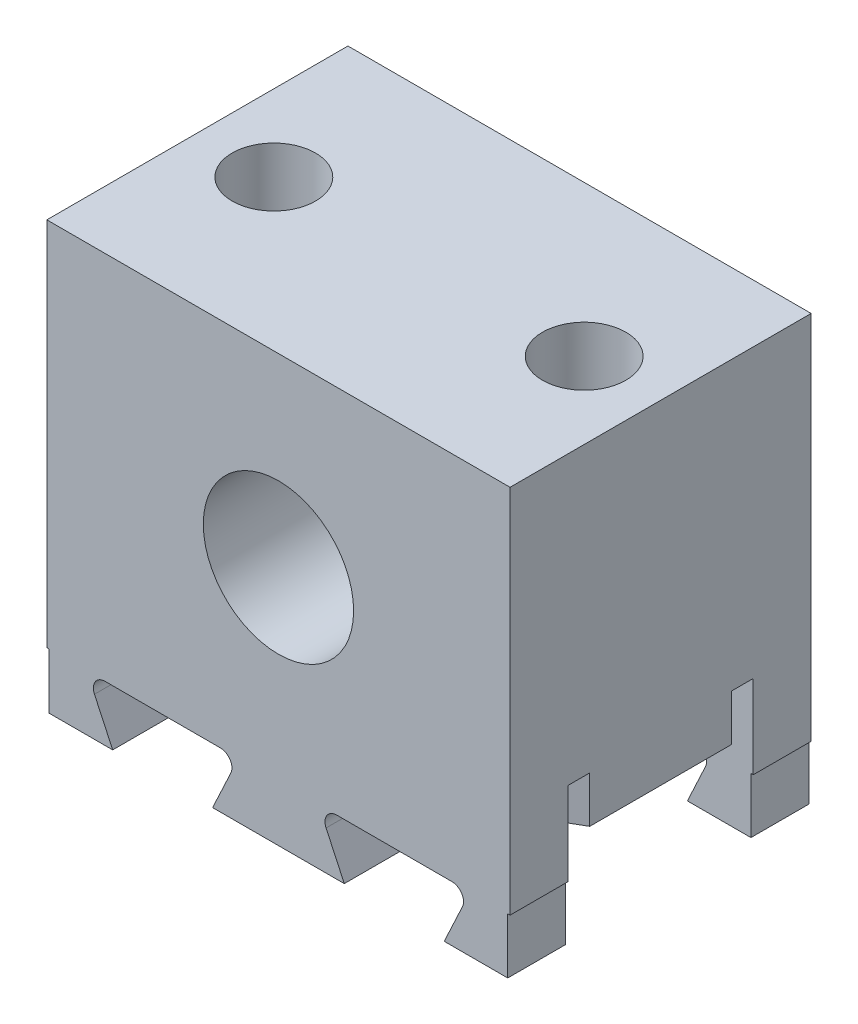
SolidWorks part; units mm, degrees
ref_plane "Front Plane" through (0, 0, 0) normal (0, 0, 1) x (1, 0, 0)
ref_plane "Top Plane" through (0, 0, 0) normal (0, 1, 0) x (1, 0, 0)
ref_plane "Right Plane" through (0, 0, 0) normal (1, 0, 0) x (0, 0, -1)
sketch "Sketch1" plane through (0, 0, 0) normal (0, 0, 1) x (1, 0, 0)
  line L1 (0, 0) -> (20, 0)
  line L2 (0, 0) -> (0, 16)
  line L3 (0, 16) -> (20, 16)
  line L4 (20, 0) -> (20, 16)
  dimension "D1" = 20
  dimension "D2" = 16
extrude "Boss-Extrude1" add sketch "Sketch1" along normal blind 13
sketch "Sketch2" plane through (0, 0, 0) normal (0, -1, 0) x (1, 0, 0)
  line L5 (0, 6.5) -> (20, 6.5) construction
  line L6 (0, 13) -> (0, 0) construction
  line L7 (20, 13) -> (20, 0) construction
  line L9 (0, 2.5) -> (20, 2.5)
  line L10 (0, 2.5) -> (0, 10.5)
  line L11 (0, 10.5) -> (20, 10.5)
  line L12 (20, 2.5) -> (20, 10.5)
  line L13 (0, 2.5) -> (20, 10.5) construction
  line L14 (0, 10.5) -> (20, 2.5) construction
  point P6 (10, 6.5)
  dimension "D1" = 8
extrude "Cut-Extrude1" cut sketch "Sketch2" against normal blind 3.6
sketch "Sketch3" plane through (0, 16, 0) normal (0, 1, 0) x (1, 0, 0)
  line L0 (0, -6.5) -> (20, -6.5) construction
  line L1 (0, -13) -> (0, 0) construction
  line L2 (20, -13) -> (20, 0) construction
  line L3 (10, 0) -> (10, -13) construction
  line L4 (20, 0) -> (0, 0) construction
  line L5 (20, -13) -> (0, -13) construction
  line L6 (1.5, -6.5) -> (1.5, 0) construction
  circle A0 centre (3.3, -6.5) radius 1.8
  circle A1 centre (16.7, -6.5) radius 1.8
  dimension "D1" = 3.6
  dimension "D2" = 1.5
extrude "Cut-Extrude2" cut sketch "Sketch3" against normal through all
sketch "Sketch4" plane through (0, 3.6, 0) normal (0, -1, 0) x (1, 0, 0)
  line L0 (3.3, 9.7344) -> (6.1011, 8.1172)
  line L1 (6.1011, 8.1172) -> (6.1011, 4.8828)
  line L2 (6.1011, 4.8828) -> (3.3, 3.2656)
  line L3 (3.3, 3.2656) -> (0.4989, 4.8828)
  line L4 (0.4989, 4.8828) -> (0.4989, 8.1172)
  line L5 (0.4989, 8.1172) -> (3.3, 9.7344)
  line L6 (3.3, 9.7344) -> (0.4989, 4.8828) construction
  line L7 (0.4989, 4.8828) -> (6.1011, 4.8828) construction
  line L8 (0.4989, 8.1172) -> (6.1011, 4.8828) construction
  line L9 (16.7, 9.7344) -> (19.5011, 8.1172)
  line L10 (19.5011, 8.1172) -> (19.5011, 4.8828)
  line L11 (19.5011, 4.8828) -> (16.7, 3.2656)
  line L12 (16.7, 3.2656) -> (13.8989, 4.8828)
  line L13 (13.8989, 4.8828) -> (13.8989, 8.1172)
  line L14 (13.8989, 8.1172) -> (16.7, 9.7344)
  line L15 (16.7, 9.7344) -> (13.8989, 4.8828) construction
  line L16 (13.8989, 4.8828) -> (19.5011, 4.8828) construction
  line L17 (13.8989, 8.1172) -> (19.5011, 4.8828) construction
  line L18 (3.3, 11.4665) -> (7.6011, 8.9832)
  line L19 (7.6011, 8.9832) -> (7.6011, 4.0168)
  line L20 (7.6011, 4.0168) -> (3.3, 1.5335)
  line L21 (3.3, 1.5335) -> (-1.0011, 4.0168)
  line L22 (-1.0011, 4.0168) -> (-1.0011, 8.9832)
  line L23 (-1.0011, 8.9832) -> (3.3, 11.4665)
  line L24 (16.7, 11.4665) -> (21.0011, 8.9832)
  line L25 (21.0011, 8.9832) -> (21.0011, 4.0168)
  line L26 (21.0011, 4.0168) -> (16.7, 1.5335)
  line L27 (16.7, 1.5335) -> (12.3989, 4.0168)
  line L28 (12.3989, 4.0168) -> (12.3989, 8.9832)
  line L29 (12.3989, 8.9832) -> (16.7, 11.4665)
  line L30 (0, 9.5612) -> (0, 3.4388)
  line L31 (0, 10.5) -> (0, 2.5) construction
  line L32 (20, 9.5612) -> (20, 3.4388)
  line L33 (20, 2.5) -> (20, 10.5) construction
  circle A0 centre (3.3, 6.5) radius 1.8 construction
  circle A1 centre (3.3, 6.5) radius 1.8 construction
  circle A2 centre (3.3, 6.5) radius 1.8 construction
  circle A3 centre (16.7, 6.5) radius 1.8 construction
  circle A4 centre (16.7, 6.5) radius 1.8 construction
  circle A5 centre (16.7, 6.5) radius 1.8 construction
  point P8 (3.3, 6.5)
  point P28 (16.7, 6.5)
  line M32 (20, 2.5) -> (20, 10.5)
  line M33 (20, 10.5) -> (0, 10.5)
  line M34 (0, 10.5) -> (0, 2.5)
  line M35 (0, 2.5) -> (20, 2.5)
  dimension "D1" = 3.2344
  dimension "D2" = 1.5
  dimension "D3" = 1.5
extrude "Boss-Extrude2" add sketch "Sketch4" along normal blind 2 contours L23 L21 L20 L19 L18 L4 L5 L0 L1 L2 L3 M34 M35 M33 | L29 L28 L27 L26 L24 L13 L14 L9 L10 L11 L12 M35 M32 M33
sketch "Sketch5" plane through (0, 0, 13) normal (0, 0, 1) x (1, 0, 0)
  line L0 (7.8341, -0.7113) -> (7, -2.5) construction
  line L1 (3, -2.5) -> (2.1659, -0.7113) construction
  line L2 (7.8341, -0.7113) -> (7, -2.5)
  line L3 (3, -2.5) -> (2.1659, -0.7113)
  line L4 (17.8341, -0.7113) -> (17, -2.5) construction
  line L5 (13, -2.5) -> (12.1659, -0.7113) construction
  line L6 (17.8341, -0.7113) -> (17, -2.5)
  line L7 (13, -2.5) -> (12.1659, -0.7113)
  line L8 (0, 0) -> (0, -2.5)
  line L9 (0, -2.5) -> (3, -2.5)
  line L10 (2.6191, 0) -> (0, 0)
  line L11 (7.3809, 0) -> (12.6191, 0)
  line L12 (7, -2.5) -> (13, -2.5)
  line L13 (17, -2.5) -> (20, -2.5)
  line L14 (20, -2.5) -> (20, 0)
  line L15 (20, 0) -> (17.3809, 0)
  arc A0 (7.8341, -0.7113) -> (7.3809, 0) centre (7.3809, -0.5) ccw construction
  arc A1 (2.6191, 0) -> (2.1659, -0.7113) centre (2.6191, -0.5) ccw construction
  arc A2 (7.8341, -0.7113) -> (7.3809, 0) centre (7.3809, -0.5) ccw
  arc A3 (2.6191, 0) -> (2.1659, -0.7113) centre (2.6191, -0.5) ccw
  arc A4 (17.8341, -0.7113) -> (17.3809, 0) centre (17.3809, -0.5) ccw construction
  arc A5 (12.6191, 0) -> (12.1659, -0.7113) centre (12.6191, -0.5) ccw construction
  arc A6 (17.8341, -0.7113) -> (17.3809, 0) centre (17.3809, -0.5) ccw
  arc A7 (12.6191, 0) -> (12.1659, -0.7113) centre (12.6191, -0.5) ccw
sketch "Sketch6" plane through (0, 0, 13) normal (0, 0, 1) x (1, 0, 0)
  line L0 (3, -2.5) -> (1.8342, 0) construction
  line L1 (2.6191, 0) -> (0, 0) construction
  line L2 (3, -2.5) -> (2.1659, -0.7113) construction
  line L3 (7, -2.5) -> (8.1658, 0) construction
  line L4 (7.3809, 0) -> (12.6191, 0) construction
  line L5 (7.8341, -0.7113) -> (7, -2.5) construction
  line L6 (13, -2.5) -> (11.8342, 0) construction
  line L7 (13, -2.5) -> (12.1659, -0.7113) construction
  line L8 (17, -2.5) -> (18.1658, 0) construction
  line L9 (20, 0) -> (17.3809, 0) construction
  line L10 (17.8341, -0.7113) -> (17, -2.5) construction
  line L12 (0, 0) -> (0, -2.5) construction
  line L13 (0, -2.5) -> (3, -2.5) construction
  line L14 (7, -2.5) -> (13, -2.5) construction
  line L15 (17, -2.5) -> (20, -2.5) construction
  line L16 (20, -2.5) -> (20, 0) construction
  line L18 (0.1, 0) -> (0.1, -2.4)
  line L19 (0.1, -2.4) -> (2.843, -2.4)
  line L20 (2.843, -2.4) -> (1.7436, -0.0423)
  line L21 (12.843, -2.4) -> (11.7436, -0.0423)
  line L22 (7.157, -2.4) -> (12.843, -2.4)
  line L23 (7.157, -2.4) -> (8.2564, -0.0423)
  line L24 (19.9, -2.4) -> (19.9, 0)
  line L25 (17.157, -2.4) -> (19.9, -2.4)
  line L26 (17.157, -2.4) -> (18.2564, -0.0423)
  line L27 (18.2564, -0.0423) -> (18.2761, 0)
  line L28 (18.2761, 0) -> (19.9, 0)
  line L29 (11.7436, -0.0423) -> (11.7239, 0)
  line L30 (8.2564, -0.0423) -> (8.2761, 0)
  line L31 (1.7436, -0.0423) -> (1.7239, 0)
  line L32 (0.1, 0) -> (1.7239, 0)
  line L33 (8.2761, 0) -> (11.7239, 0)
  dimension "D1" = 0.1
  dimension "D2" = 0.1
  dimension "D3" = 0.1
extrude "Boss-Extrude3" add sketch "Sketch6" against normal up to surface (13 mm away) up to face at (10, 8, 0)
sketch "Sketch7" plane through (0, -2.4, 0) normal (0, -1, 0) x (1, 0, 0)
  line L0 (0, 10.5) -> (0, 9.5612) construction
  line L1 (0, 10.5) -> (0, 9.5612) construction
  line L2 (20, 2.5) -> (20, 3.4388) construction
  line L3 (20, 2.5) -> (20, 3.4388) construction
  line L5 (0, 10.5) -> (20, 10.5)
  line L6 (0, 10.5) -> (0, 2.5)
  line L7 (0, 2.5) -> (20, 2.5)
  line L8 (20, 10.5) -> (20, 2.5)
extrude "Cut-Extrude3" cut sketch "Sketch7" against normal up to surface (4 mm away) up to face at (16.4497, 1.6, 6.5)
fillet "Fillet1" radius 0.5 4 edges at (18.2761, 0, 11.75) (8.2761, 0, 11.75) (11.7239, 0, 11.75) (1.7239, 0, 11.75)
sketch "Sketch8" plane through (0, 0, 13) normal (0, 0, 1) x (1, 0, 0)
  circle A0 centre (10, 8) radius 2.53 construction
  circle A1 centre (10, 8) radius 2.53 construction
  circle A2 centre (10, 8) radius 3.245
  dimension "D1" = 6.49
extrude "Cut-Extrude4" cut sketch "Sketch8" against normal through all
equation "\"offset_fit\"= 0.10"
equation "\"D1@Sketch6\"=\"offset_fit\""
equation "\"D2@Sketch6\"=\"offset_fit\""
equation "\"D3@Sketch6\"=\"offset_fit\""
